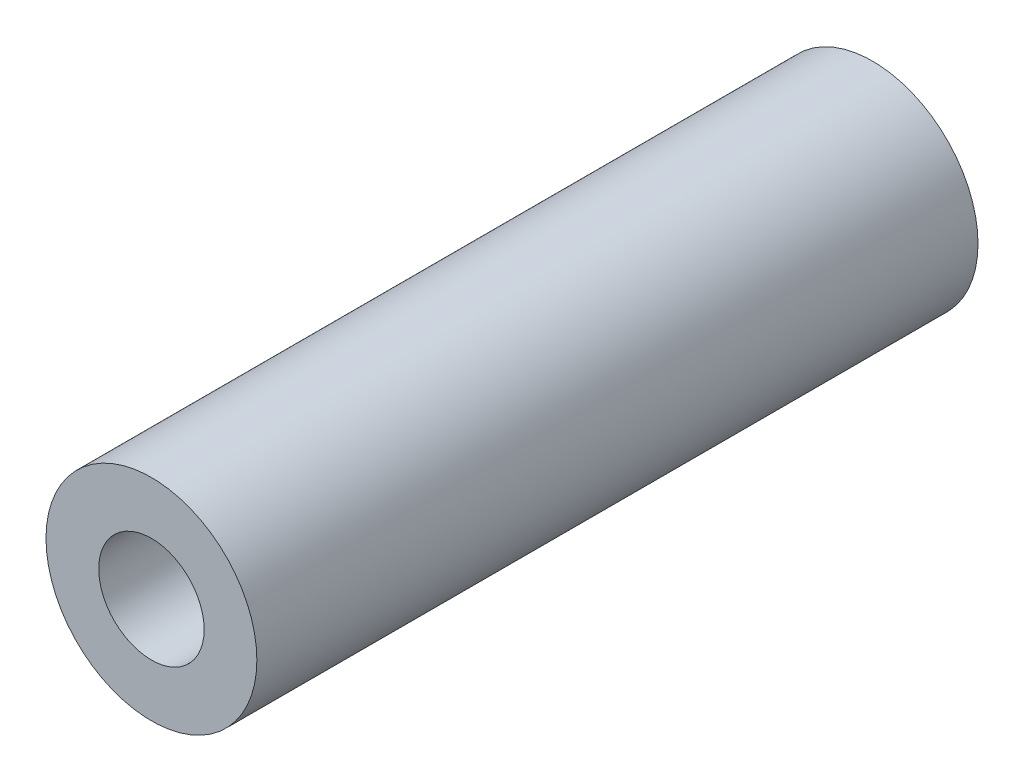
SolidWorks part; units mm, degrees
ref_plane "Front Plane" through (0, 0, 0) normal (0, 0, 1) x (1, 0, 0)
ref_plane "Top Plane" through (0, 0, 0) normal (0, 1, 0) x (1, 0, 0)
ref_plane "Right Plane" through (0, 0, 0) normal (1, 0, 0) x (0, 0, -1)
sketch "Sketch2" plane through (0, 0, 0) normal (0, 0, 1) x (1, 0, 0)
  circle A0 centre (0, 0) radius 6.35
  circle A1 centre (0, 0) radius 3.175
  dimension "D1" = 12.7
  dimension "D2" = 6.35
extrude "Boss-Extrude1" add sketch "Sketch2" along normal blind 43.434
